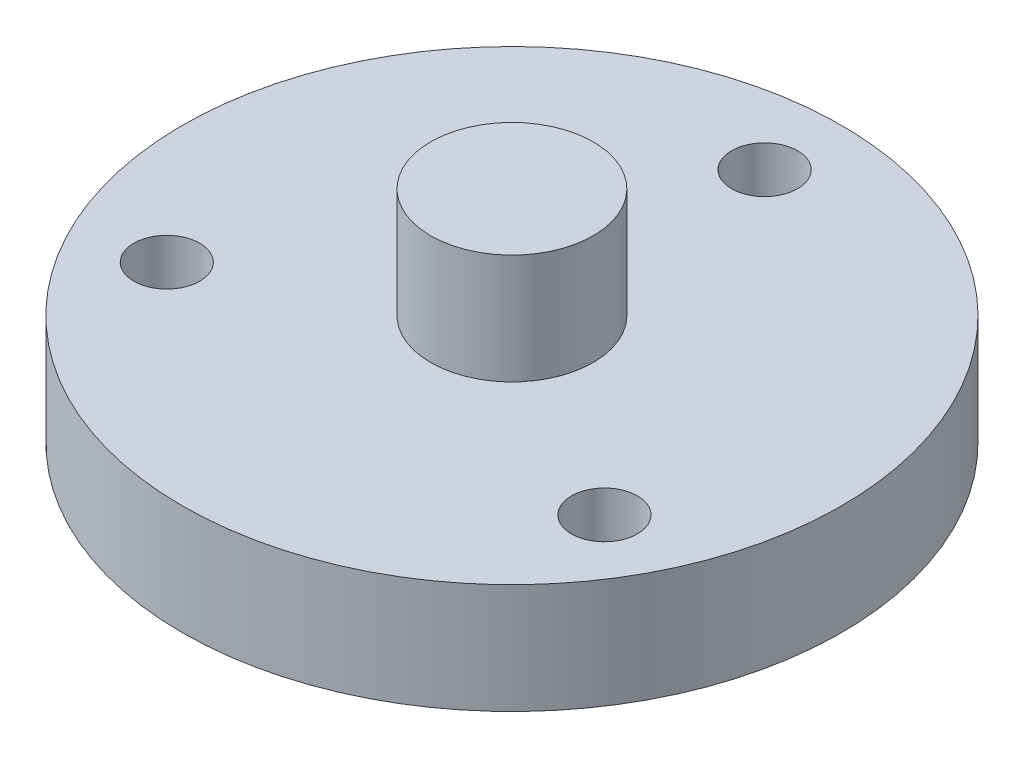
SolidWorks part; units mm, degrees
ref_plane "Plan de face" through (0, 0, 0) normal (0, 0, 1) x (1, 0, 0)
ref_plane "Plan de dessus" through (0, 0, 0) normal (0, 1, 0) x (1, 0, 0)
ref_plane "Plan de droite" through (0, 0, 0) normal (1, 0, 0) x (0, 0, -1)
sketch "Esquisse1" plane through (0, 0, 0) normal (0, 0, 1) x (1, 0, 0)
  line L0 (0, 0) -> (30, 0)
  line L1 (30, 0) -> (30, 10)
  line L2 (30, 10) -> (7.4, 10)
  line L3 (7.4, 10) -> (7.4, 20)
  line L4 (7.4, 20) -> (0, 20)
  line L5 (0, 30.2514) -> (0, -22.5419) construction
  line L6 (0, 0) -> (0, 20)
  dimension "D1" = 30
  dimension "D2" = 10
  dimension "D3" = 7.4
  dimension "D4" = 20
revolve "Révolution1" add sketch "Esquisse1" angle 360 about L5
sketch "Esquisse3" plane through (0, 10, 0) normal (0, 1, 0) x (1, 0, 0)
  line L0 (0, 0) -> (0, 31.2104) construction
  line L1 (0, 0) -> (33.7001, -19.4568) construction
  line L2 (0, 0) -> (-33.5186, -19.352) construction
  circle A0 centre (0, 23) radius 3
  circle A1 centre (19.9186, -11.5) radius 3
  circle A2 centre (-19.9186, -11.5) radius 3
  dimension "D3" = 6
  dimension "D4" = 23
  dimension "D5" = 23
  dimension "D6" = 23
  dimension "D1" = 120
  dimension "D2" = 120
extrude "Enlèv. mat.-Extru.1" cut sketch "Esquisse3" against normal through all
